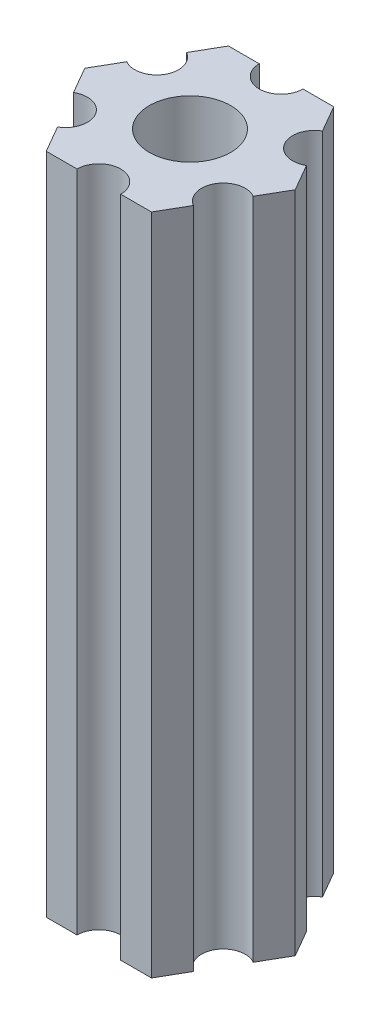
SolidWorks part; units mm, degrees
material "Churro - 6005A-T61"
ref_plane "Plano frontal" through (0, 0, 0) normal (0, 0, 1) x (1, 0, 0)
ref_plane "Plano superior" through (0, 0, 0) normal (0, 1, 0) x (1, 0, 0)
ref_plane "Plano direito" through (0, 0, 0) normal (1, 0, 0) x (0, 0, -1)
ref_plane "Plano1" through (0, -34.5, 0) normal (0, -1, 0) x (1, 0, 0)
sketch "Esboço1" plane through (0, -34.5, 0) normal (0, -1, 0) x (1, 0, 0)
  line L0 (77.0627, 17.174) -> (78.1169, 19)
  line L1 (78.1169, 19) -> (77.0627, 20.826)
  line L2 (75.5627, 23.424) -> (74.5084, 25.25)
  line L3 (74.5084, 25.25) -> (72.4, 25.25)
  line L4 (69.4, 25.25) -> (67.2916, 25.25)
  line L5 (67.2916, 25.25) -> (66.2373, 23.424)
  line L6 (64.7373, 20.826) -> (63.6831, 19)
  line L7 (63.6831, 19) -> (64.7373, 17.174)
  line L8 (66.2373, 14.576) -> (67.2916, 12.75)
  line L9 (67.2916, 12.75) -> (69.4, 12.75)
  line L10 (72.4, 12.75) -> (74.5084, 12.75)
  line L11 (74.5084, 12.75) -> (75.5627, 14.576)
  circle A0 centre (70.9, 19) radius 2.79
  arc A1 (77.0627, 20.826) -> (75.5627, 23.424) centre (76.3127, 22.125) cw
  arc A2 (72.4, 25.25) -> (69.4, 25.25) centre (70.9, 25.25) cw
  arc A3 (66.2373, 23.424) -> (64.7373, 20.826) centre (65.4873, 22.125) cw
  arc A4 (64.7373, 17.174) -> (66.2373, 14.576) centre (65.4873, 15.875) cw
  arc A5 (69.4, 12.75) -> (72.4, 12.75) centre (70.9, 12.75) cw
  arc A6 (75.5627, 14.576) -> (77.0627, 17.174) centre (76.3127, 15.875) cw
extrude "Ressalto-extrusão1" add sketch "Esboço1" against normal blind 45.5
